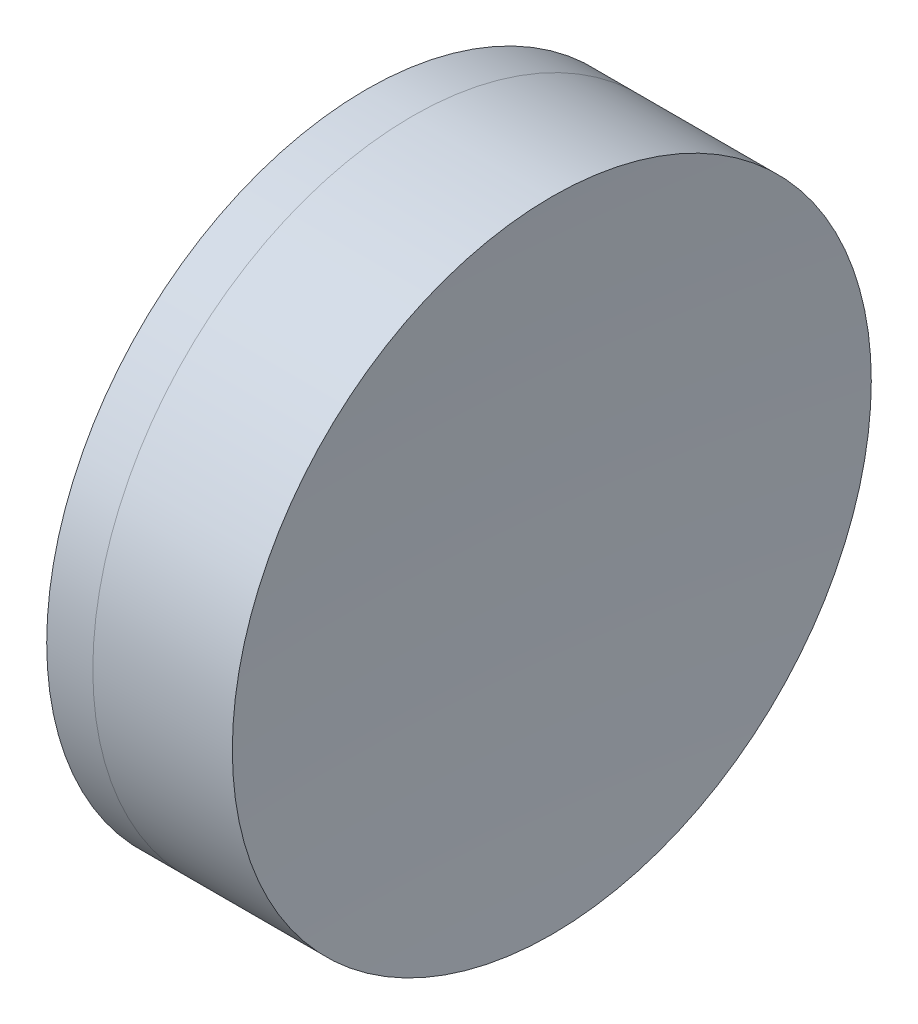
SolidWorks part; units mm, degrees
ref_plane "前视基准面" through (0, 0, 0) normal (0, 0, 1) x (1, 0, 0)
ref_plane "上视基准面" through (0, 0, 0) normal (0, 1, 0) x (1, 0, 0)
ref_plane "右视基准面" through (0, 0, 0) normal (1, 0, 0) x (0, 0, -1)
sketch "草图1" plane through (0, 0, 0) normal (0, 1, 0) x (1, 0, 0)
  line L0 (-0.8161, 0) -> (45.8933, 0) construction
  line L1 (35.7956, -12.7) -> (37.629, -12.7)
  line L2 (35.7956, 12.7) -> (37.629, 12.7)
  arc A0 (37.629, -12.7) -> (37.629, 12.7) centre (15.0794, 0) ccw
  arc A1 (35.7956, 12.7) -> (35.7956, -12.7) centre (54.8994, 0) ccw
  point P10 (31.9594, 0)
  point P11 (40.9594, 0)
  dimension "D3" = 22.94
  dimension "D4" = 25.88
  dimension "D1" = 12.7
  dimension "D2" = 12.7
  dimension "D5" = 9
revolve "旋转1" add sketch "草图1" angle 360 about L0
sketch "草图2" plane through (0, 0, 0) normal (0, 1, 0) x (1, 0, 0)
  line L0 (-0.5519, 0) -> (45.4982, 0) construction
  line L2 (37.629, 12.7) -> (43.1744, 12.7)
  line L3 (37.629, -12.7) -> (43.1744, -12.7)
  arc A0 (43.1744, 12.7) -> (43.1744, -12.7) centre (237.2994, 0) ccw
  arc A1 (37.629, -12.7) -> (37.629, 12.7) centre (15.0794, 0) ccw construction
  arc A2 (37.629, -12.7) -> (37.629, 12.7) centre (15.0794, 0) ccw
  point P4 (40.9594, 0)
  point P8 (42.7594, 0)
  dimension "D1" = 194.54
  dimension "D2" = 1.8
revolve "旋转2" add sketch "草图2" angle 360 about L0
